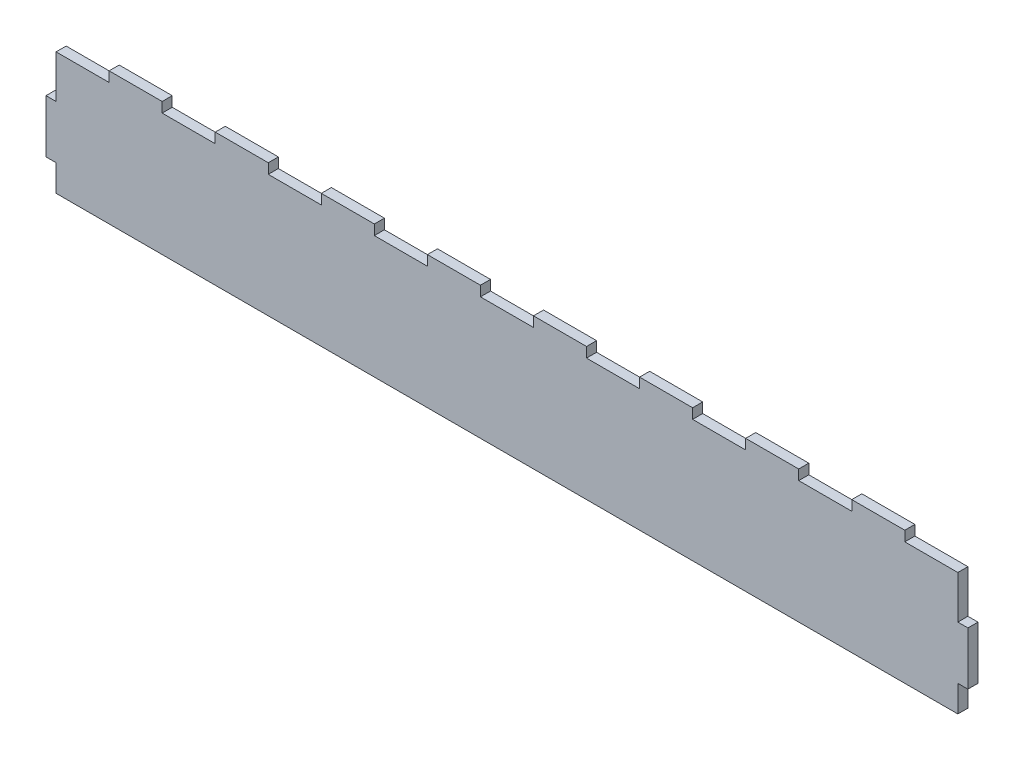
SolidWorks part; units mm, degrees
material "1060 Alloy"
ref_plane "Front Plane" through (0, 0, 0) normal (0, 0, 1) x (1, 0, 0)
ref_plane "Top Plane" through (0, 0, 0) normal (0, 1, 0) x (1, 0, 0)
ref_plane "Right Plane" through (0, 0, 0) normal (1, 0, 0) x (0, 0, -1)
sketch "Sketch1" plane through (0, 0, 0) normal (0, 0, 1) x (1, 0, 0)
  line L0 (527.05, 12.7) -> (527.05, 0)
  line L1 (0, 0) -> (622.3, 0) construction
  line L2 (0, 0) -> (0, 63.5) construction
  line L3 (0, 63.5) -> (95.25, 63.5) construction
  line L4 (622.3, 0) -> (622.3, 63.5) construction
  line L5 (120.65, 63.5) -> (146.05, 63.5)
  line L6 (95.25, 58.674) -> (95.25, 38.1)
  line L7 (95.25, 0) -> (527.05, 0)
  line L8 (527.05, 58.674) -> (527.05, 38.1)
  line L9 (527.05, 38.1) -> (531.876, 38.1)
  line L10 (95.25, 12.7) -> (95.25, 0)
  line L11 (527.05, 12.7) -> (531.876, 12.7)
  line L12 (531.876, 38.1) -> (531.876, 12.7)
  line L13 (95.25, 38.1) -> (90.424, 38.1)
  line L14 (146.05, 58.674) -> (171.45, 58.674)
  line L15 (95.25, 12.7) -> (90.424, 12.7)
  line L16 (90.424, 38.1) -> (90.424, 12.7)
  line L17 (222.25, 63.5) -> (247.65, 63.5)
  line L19 (95.25, 58.674) -> (120.65, 58.674)
  line L20 (120.65, 63.5) -> (120.65, 58.674)
  line L21 (171.45, 63.5) -> (171.45, 58.674)
  line L22 (146.05, 63.5) -> (146.05, 58.674)
  line L23 (196.85, 58.674) -> (222.25, 58.674)
  line L24 (222.25, 63.5) -> (222.25, 58.674)
  line L25 (196.85, 63.5) -> (196.85, 58.674)
  line L26 (247.65, 58.674) -> (273.05, 58.674)
  line L27 (273.05, 63.5) -> (273.05, 58.674)
  line L28 (247.65, 63.5) -> (247.65, 58.674)
  line L29 (298.45, 58.674) -> (323.85, 58.674)
  line L30 (323.85, 63.5) -> (323.85, 58.674)
  line L31 (298.45, 63.5) -> (298.45, 58.674)
  line L32 (349.25, 58.674) -> (374.65, 58.674)
  line L33 (374.65, 63.5) -> (374.65, 58.674)
  line L34 (349.25, 63.5) -> (349.25, 58.674)
  line L35 (400.05, 58.674) -> (425.45, 58.674)
  line L36 (425.45, 63.5) -> (425.45, 58.674)
  line L37 (400.05, 63.5) -> (400.05, 58.674)
  line L38 (450.85, 58.674) -> (476.25, 58.674)
  line L39 (476.25, 63.5) -> (476.25, 58.674)
  line L40 (450.85, 63.5) -> (450.85, 58.674)
  line L41 (501.65, 58.674) -> (527.05, 58.674)
  line L43 (501.65, 63.5) -> (501.65, 58.674)
  line L44 (527.05, 63.5) -> (622.3, 63.5) construction
  line L45 (476.25, 63.5) -> (501.65, 63.5) construction
  line L46 (476.25, 63.5) -> (501.65, 63.5)
  line L47 (425.45, 63.5) -> (450.85, 63.5) construction
  line L48 (425.45, 63.5) -> (450.85, 63.5)
  line L49 (374.65, 63.5) -> (400.05, 63.5) construction
  line L50 (374.65, 63.5) -> (400.05, 63.5)
  line L51 (323.85, 63.5) -> (349.25, 63.5) construction
  line L52 (323.85, 63.5) -> (349.25, 63.5)
  line L53 (273.05, 63.5) -> (298.45, 63.5) construction
  line L54 (273.05, 63.5) -> (298.45, 63.5)
  line L55 (222.25, 63.5) -> (247.65, 63.5) construction
  line L56 (171.45, 63.5) -> (196.85, 63.5) construction
  line L57 (171.45, 63.5) -> (196.85, 63.5)
  line L58 (120.65, 63.5) -> (146.05, 63.5) construction
  line L59 (527.05, 63.5) -> (527.05, 58.674) [skipped]
  dimension "D1" = 63.5
  dimension "D2" = 622.3
  dimension "D3" = 95.25
  dimension "D4" = 95.25
  dimension "D5" = 25.4
  dimension "D6" = 25.4
  dimension "D7" = 4.826
  dimension "D8" = 25.4
  dimension "D9" = 25.4
  dimension "D10" = 4.826
  dimension "D11" = 4.826
  dimension "D12" = 25.4
  dimension "D13" = 9
extrude "Boss-Extrude1" add sketch "Sketch1" along normal blind 4.826
equation "\"sheet width\"= .19"
equation "\"width\"= 24.5"
equation "\"length\"= 34.5"
equation "\"standoff hole size\"= .5"
equation "\"ground clearence\"= 3"
equation "\"small drive pulley\"= 74.55mm"
equation "\"large drive pulley\"= 150.95mm"
equation "\"drive axle hole size\"= .5"
equation "\"front pulley clearence\"= 1"
equation "\"center support location\"= 19"
equation "\"inner to outer wall size\"= 3.75"
equation "\"D2@Sketch1\"=\"width\""
equation "\"D3@Sketch1\"=\"inner to outer wall size\""
equation "\"D4@Sketch1\"=\"inner to outer wall size\""
equation "\"D7@Sketch1\"=\"sheet width\""
equation "\"D10@Sketch1\"=\"sheet width\""
equation "\"D11@Sketch1\"=\"sheet width\""
equation "\"D1@Boss-Extrude1\"=\"sheet width\""
